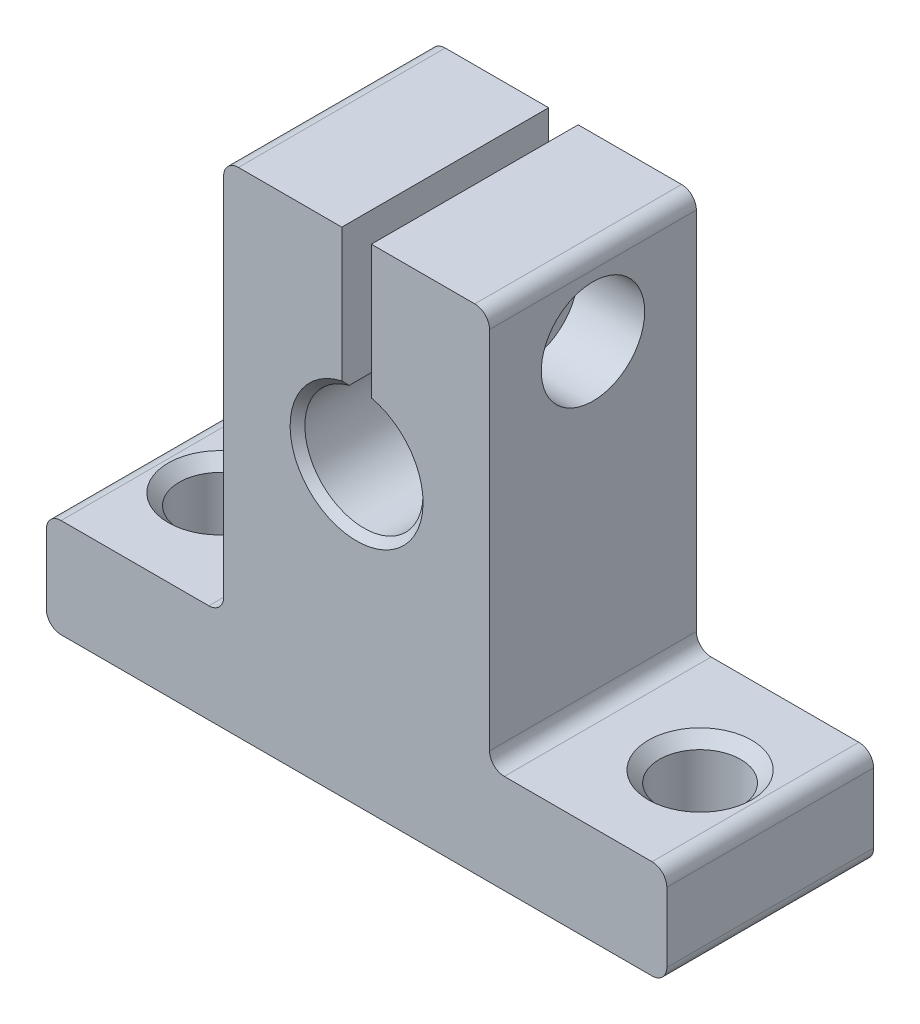
SolidWorks part; units mm, degrees
material "1060 Alloy"
ref_plane "Plane1" through (0, 0, 0) normal (0, 0, 1) x (1, 0, 0)
ref_plane "Plane2" through (0, 0, 0) normal (0, 1, 0) x (1, 0, 0)
ref_plane "Plane3" through (0, 0, 0) normal (1, 0, 0) x (0, 0, -1)
sketch "Sketch1" plane through (0, 0, 0) normal (0, 0, 1) x (1, 0, 0)
  line L0 (-21, -20) -> (21, -20)
  line L1 (21, -20) -> (21, -13.3)
  line L2 (21, -13.3) -> (9, -13.3)
  line L3 (9, -13.3) -> (9, 13.4)
  line L4 (9, 13.4) -> (1, 13.4)
  line L5 (1, 13.4) -> (1, 3.873)
  line L6 (-1, 3.873) -> (-1, 13.4)
  line L7 (-1, 13.4) -> (-9, 13.4)
  line L8 (-9, 13.4) -> (-9, -13.3)
  line L9 (-9, -13.3) -> (-21, -13.3)
  line L10 (-21, -13.3) -> (-21, -20)
  line L11 (1, 13.4) -> (-1, 13.4) construction
  line L12 (0, 13.4) -> (0, 0) construction
  arc A2 (-1, 3.873) -> (1, 3.873) centre (0, 0) ccw
  dimension "D7" = 8
  dimension "D8" = 20
  dimension "D1" = 42
  dimension "D2" = 6.7
  dimension "D3" = 12
  dimension "D4" = 12
  dimension "D5" = 8
  dimension "D6" = 8
  dimension "D9" = 33.4
  dimension "D10" = 26.7
extrude "Boss-Extrude1" add sketch "Sketch1" along normal blind 14
fillet "Fillet1" radius 1 8 edges at (21, -20, 7) (-21, -20, 7) (-9, -13.3, 7) (9, -13.3, 7) (9, 13.4, 7) (-9, 13.4, 7) (-21, -13.3, 7) (21, -13.3, 7)
hole_wizard "CBORE for M5 Hex Head Bolt1" positions "Sketch4" profile "Sketch3" counterbore size "M5" standard "ISO" end condition up to next
sketch "Sketch4" plane through (9, 0, 0) normal (1, 0, 0) x (0, 0, -1)
  line L0 (0, -13.3) -> (-14, -13.3) construction
  line L1 (-14, -12.3) -> (-14, 12.4) construction
  point P0 (-7, 8.2)
  dimension "D1" = 21.5
  dimension "D2" = 7
sketch "Sketch3" plane through (9, 8.2, 7) normal (0, 1, 0) x (0, 0, -1)
  line L0 (0, 0) -> (0, 8)
  line L1 (0, 8) -> (2, 8)
  line L3 (2, 8) -> (2, 4.5)
  line L4 (2, 4.5) -> (3.5, 4.5)
  line L5 (3.5, 4.5) -> (3.5, 0)
  line L7 (3.5, 0) -> (0, 0)
  line L11 (0, -6.35) -> (0, 107.95) construction
  dimension "Thru Hole Dia." = 4
  dimension "Thru Hole Depth" = 8
  dimension "C'Bore Dia." = 7
  dimension "C'Bore Depth" = 4.5
hole_wizard "M5 Tapped Hole1" positions "Sketch5" profile "Sketch6" tap size "M5" standard "ISO" end condition up to next
sketch "Sketch5" plane through (-9, 0, 0) normal (-1, 0, 0) x (0, 0, 1)
  line L0 (14, 12.4) -> (14, -12.3) construction
  line L2 (14, -13.3) -> (0, -13.3) construction
  point P0 (7, 8.2)
  dimension "D1" = 7
  dimension "D2" = 21.5
sketch "Sketch6" plane through (-9, 8.2, 7) normal (0, 1, 0) x (0, 0, 1)
  line L0 (0, 0) -> (0, 8)
  line L1 (0, 8) -> (1.75, 8)
  line L2 (1.75, 8) -> (1.75, 1)
  line L3 (1.75, 1) -> (2.75, 0)
  line L5 (2.75, 0) -> (0, 0)
  line L6 (-1.75, 1) -> (-2.75, 0) construction
  line L11 (0, -6.35) -> (0, 107.95) construction
  dimension "Thru Tap Drill Dia." = 3.5
  dimension "Thru Tap Drill Depth" = 8
  dimension "Near C'Sink Dia." = 5.5
  dimension "Near C'Sink Angle" = 90
cosmetic thread "Hole Thread1" parameters "D2"=5
hole_wizard "CSK for M5 Countersunk Flat Head Screw2" positions "Sketch7" profile "Sketch8" countersink size "M5" standard "ISO" end condition up to next
sketch "Sketch7" plane through (0, -13.3, 0) normal (0, 1, 0) x (1, 0, 0)
  line L0 (21, 0) -> (21, -14) construction
  line L1 (20, 0) -> (10, 0) construction
  point P0 (16.25, -7)
  dimension "D1" = 4.75
  dimension "D2" = 7
sketch "Sketch8" plane through (16.25, -13.3, 7) normal (1, 0, 0) x (0, 0, 1)
  line L0 (0, 0) -> (0, 6.7)
  line L1 (0, 6.7) -> (3.5, 6.7)
  line L2 (2.75, 5.95) -> (2.75, 0.75)
  line L3 (2.75, 0.75) -> (3.5, 0)
  line L5 (3.5, 0) -> (0, 0)
  line L6 (-2.75, 0.75) -> (-3.5, 0) construction
  line L7 (3.5, 6.7) -> (2.75, 5.95)
  line L8 (-3.5, 6.7) -> (-2.75, 5.95) construction
  line L11 (0, -6.35) -> (0, 107.95) construction
  dimension "Thru Hole Dia." = 5.5
  dimension "Thru Hole Depth" = 6.7
  dimension "Near C'Sink Dia." = 7
  dimension "Near C'Sink Angle" = 90
  dimension "Far C'Sink Dia." = 7
  dimension "Far C'Sink Angle" = 90
hole_wizard "CSK for M5 Countersunk Flat Head Screw3" positions "Sketch9" profile "Sketch10" countersink size "M5" standard "ISO" end condition up to next
sketch "Sketch9" plane through (0, -13.3, 0) normal (0, 1, 0) x (1, 0, 0)
  line L0 (-10, 0) -> (-20, 0) construction
  line L1 (-21, -14) -> (-21, 0) construction
  point P0 (-16.25, -7)
  dimension "D1" = 7
  dimension "D2" = 4.75
sketch "Sketch10" plane through (-16.25, -13.3, 7) normal (1, 0, 0) x (0, 0, 1)
  line L0 (0, 0) -> (0, 6.7)
  line L1 (0, 6.7) -> (3.5, 6.7)
  line L2 (2.75, 5.95) -> (2.75, 0.75)
  line L3 (2.75, 0.75) -> (3.5, 0)
  line L5 (3.5, 0) -> (0, 0)
  line L6 (-2.75, 0.75) -> (-3.5, 0) construction
  line L7 (3.5, 6.7) -> (2.75, 5.95)
  line L8 (-3.5, 6.7) -> (-2.75, 5.95) construction
  line L11 (0, -6.35) -> (0, 107.95) construction
  dimension "Thru Hole Dia." = 5.5
  dimension "Thru Hole Depth" = 6.7
  dimension "Near C'Sink Dia." = 7
  dimension "Near C'Sink Angle" = 90
  dimension "Far C'Sink Dia." = 7
  dimension "Far C'Sink Angle" = 90
chamfer "Chamfer1" distance 0.5 angle 45 2 edges at (0, -4, 14) (0, -4, 0)
